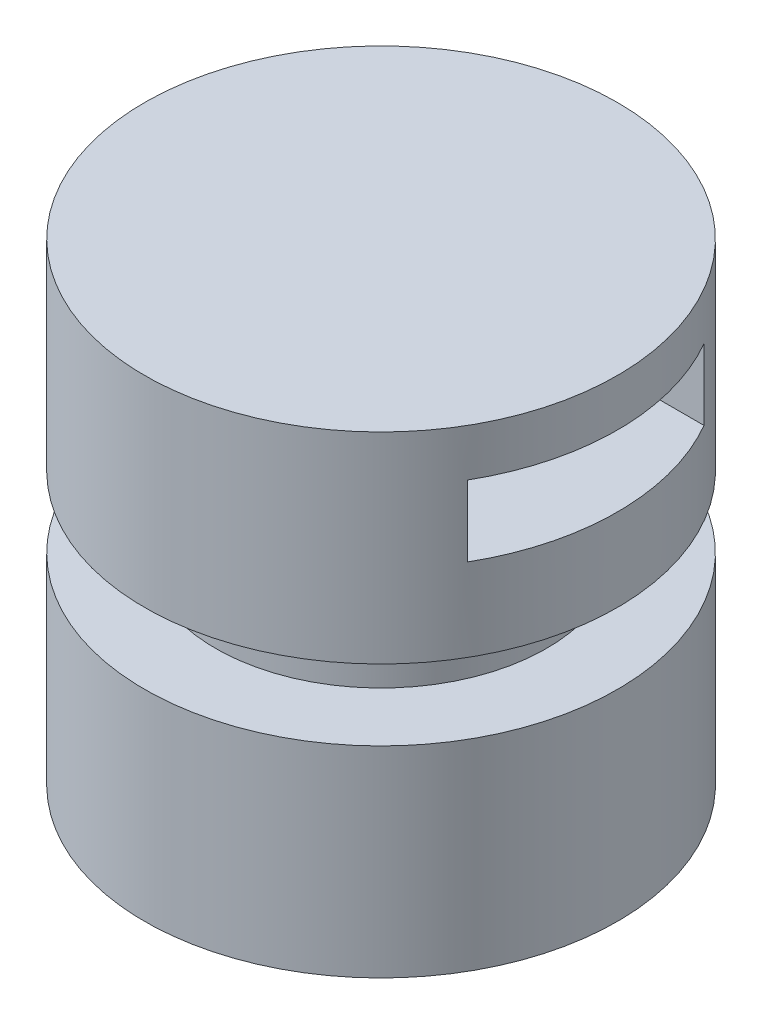
SolidWorks part; units mm, degrees
ref_plane "Front Plane" through (0, 0, 0) normal (0, 0, 1) x (1, 0, 0)
ref_plane "Top Plane" through (0, 0, 0) normal (0, 1, 0) x (1, 0, 0)
ref_plane "Right Plane" through (0, 0, 0) normal (1, 0, 0) x (0, 0, -1)
sketch "Sketch1" plane through (0, 0, 0) normal (0, 0, 1) x (1, 0, 0)
  line L1 (0, 0) -> (100, 0)
  line L2 (0, 0) -> (0, 200)
  line L3 (0, 200) -> (100, 200)
  line L4 (100, 0) -> (100, 200)
  dimension "D1" = 200
  dimension "D2" = 100
revolve "Revolve1" add sketch "Sketch1" angle 360 about L2
sketch "Sketch2" plane through (0, 0, 0) normal (1, 0, 0) x (0, 0, -1)
  line L0 (100, 0) -> (100, 200) construction
  line L1 (100, 85) -> (70, 85)
  line L2 (100, 85) -> (100, 115)
  line L3 (100, 115) -> (70, 115)
  line L4 (70, 85) -> (70, 115)
  line L5 (100, 100) -> (70, 100)
  line L6 (0, 200) -> (0, 0)
  line L7 (100, 200) -> (-100, 200) construction
  dimension "D1" = 100
  dimension "D2" = 30
revolve "Cut-Revolve1" cut sketch "Sketch2" angle 360 about L6
sketch "Sketch3" plane through (0, 0, 0) normal (1, 0, 0) x (0, 0, -1)
  line L0 (100, 200) -> (-100, 200) construction
  line L1 (-50, 150) -> (50, 150)
  line L2 (-50, 150) -> (-50, 180)
  line L3 (-50, 180) -> (50, 180)
  line L4 (50, 150) -> (50, 180)
  line L5 (0, 150) -> (0, 180) construction
  line L6 (0, 200) -> (0, 0) construction
  line L7 (0, 200) -> (0, 114.6846) construction
  dimension "D1" = 100
  dimension "D2" = 30
  dimension "D3" = 20
extrude "Cut-Extrude1" cut sketch "Sketch3" against normal through all and the other way through all
